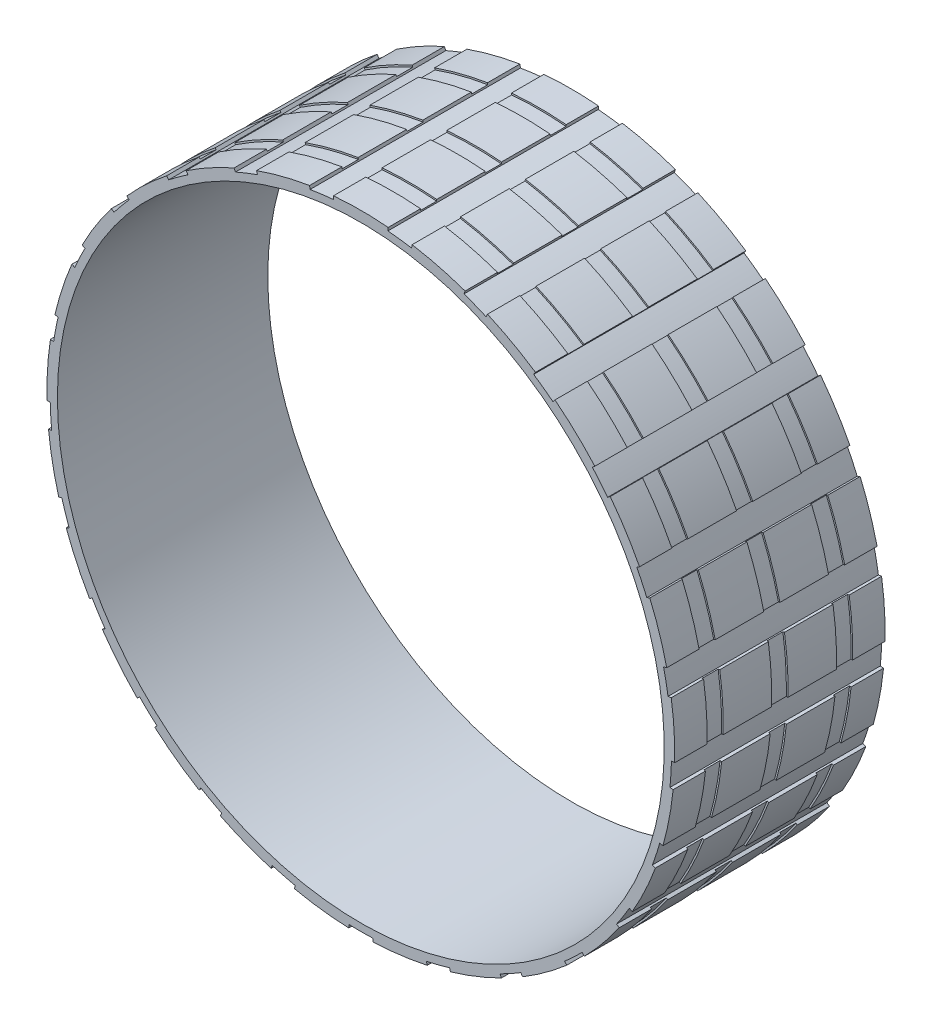
SolidWorks part; units mm, degrees
ref_plane "Front Plane" through (0, 0, 0) normal (0, 0, 1) x (1, 0, 0)
ref_plane "Top Plane" through (0, 0, 0) normal (0, 1, 0) x (1, 0, 0)
ref_plane "Right Plane" through (0, 0, 0) normal (1, 0, 0) x (0, 0, -1)
sketch "Sketch1" plane through (0, 0, 0) normal (0, 0, 1) x (1, 0, 0)
  circle A0 centre (0, 0) radius 18.75
  dimension "D1" = 37.5
sketch "Sketch2" plane through (0, 0, 0) normal (0, 0, 1) x (1, 0, 0)
  circle A0 centre (0, 0) radius 19.2
  circle A1 centre (0, 0) radius 18.75 construction
  dimension "D1" = 0.45
extrude "Boss-Extrude1" add sketch "Sketch2" along normal mid plane 13 contours A0
extrude "Cut-Extrude1" cut sketch "Sketch1" against normal up to next and the other way up to next
sketch "Sketch3" plane through (0, 0, 0) normal (1, 0, 0) x (0, 0, -1)
  line L0 (6.5, 19.2) -> (6.5, 19.4)
  line L1 (6.5, 19.4) -> (-6.5, 19.4) construction
  line L2 (0, 23.9063) -> (0, 16.4242) construction
  line L3 (6.5, 19.4) -> (4.5, 19.4)
  line L4 (3.5, 19.4) -> (0.5, 19.4)
  line L5 (-0.5, 19.4) -> (-3.5, 19.4)
  line L6 (-4.5, 19.4) -> (-6.5, 19.4)
  line L7 (6.5, 19.3) -> (-6.5, 19.3) construction
  line L8 (4.5, 19.4) -> (4.5, 19.3)
  line L9 (4.5, 19.3) -> (3.5, 19.3)
  line L10 (3.5, 19.3) -> (3.5, 19.4)
  line L11 (0.5, 19.4) -> (0.5, 19.3)
  line L12 (0.5, 19.3) -> (-0.5, 19.3)
  line L13 (-0.5, 19.3) -> (-0.5, 19.4)
  line L14 (-3.5, 19.4) -> (-3.5, 19.3)
  line L15 (-3.5, 19.3) -> (-4.5, 19.3)
  line L16 (-4.5, 19.3) -> (-4.5, 19.4)
  line L17 (-15.3676, 0) -> (17.3096, 0) construction
  line L26 (-6.5, 19.4) -> (-6.5, 19.2)
  line L27 (-6.5, 19.2) -> (6.5, 19.2)
  point P10 (4, 19.3)
  point P20 (0, 19.3)
  dimension "D2" = 1
  dimension "D1" = 0.2
  dimension "D3" = 4
revolve "Revolve1" add sketch "Sketch3" angle 10 mid plane about L17
pattern_circular "CirPattern1" count 25 over 360 about axis through (0, 0, 0) along (0, 0, 1) of "Revolve1"
